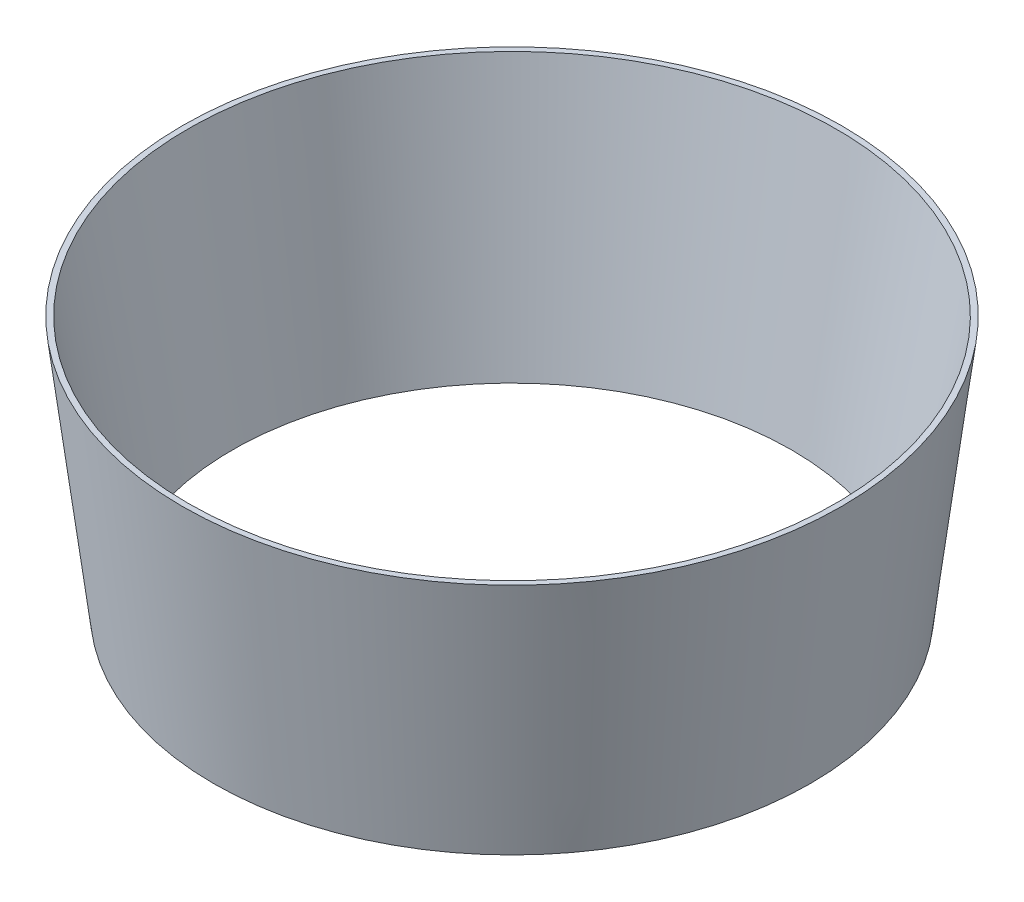
SolidWorks part; units mm, degrees
ref_plane "前视基准面" through (0, 0, 0) normal (0, 0, 1) x (1, 0, 0)
ref_plane "上视基准面" through (0, 0, 0) normal (0, 1, 0) x (1, 0, 0)
ref_plane "右视基准面" through (0, 0, 0) normal (1, 0, 0) x (0, 0, -1)
sketch "草图1" plane through (0, 0, 0) normal (0, 1, 0) x (1, 0, 0)
  circle A0 centre (0, 0) radius 802
  dimension "D1" = 1604
ref_plane "基准面4" through (0, 687.83, 0) normal (0, 1, 0) x (1, 0, 0)
sketch "草图2" plane through (0, 687.83, 0) normal (0, 1, 0) x (1, 0, 0)
  circle A0 centre (0, 0) radius 886.455
  dimension "D1" = 1772.91
loft "放样1" add profiles "草图1", "草图2"
sketch "草图3" plane through (0, 0, 0) normal (0, -1, 0) x (1, 0, 0)
  circle A0 centre (0, 0) radius 752
  dimension "D1" = 1504
sketch "草图4" plane through (0, 687.83, 0) normal (0, 1, 0) x (1, 0, 0)
  circle A0 centre (0, 0) radius 871.455
  dimension "D1" = 1742.91
loft "切除-放样1" cut profiles "草图4", "草图3"
